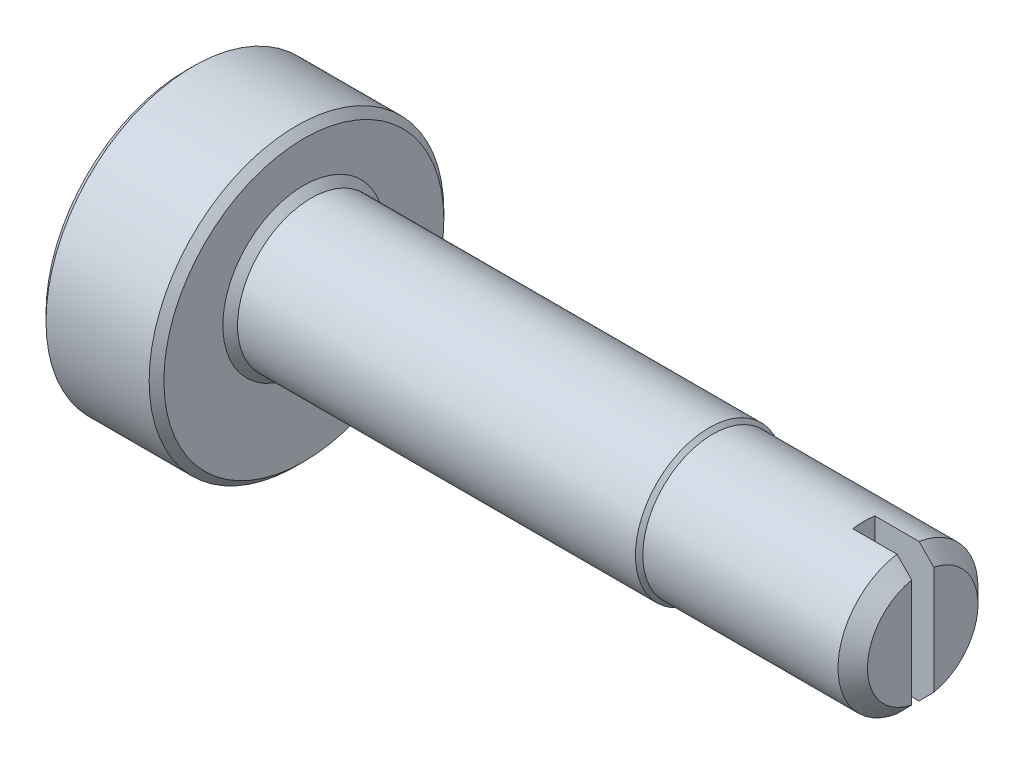
SolidWorks part; units mm, degrees
ref_plane "Спереди" through (0, 0, 0) normal (0, 0, 1) x (1, 0, 0)
ref_plane "Сверху" through (0, 0, 0) normal (0, 1, 0) x (1, 0, 0)
ref_plane "Справа" through (0, 0, 0) normal (1, 0, 0) x (0, 0, -1)
sketch "Эскиз1" plane through (0, 0, 0) normal (0, 0, 1) x (1, 0, 0)
  line L0 (0, 0) -> (0, 2.5)
  line L1 (0, 2.5) -> (1.6, 2.5)
  line L2 (1.6, 2.5) -> (1.6, 1.1)
  line L3 (1.7, 1) -> (7.1, 1)
  line L4 (10, 0.95) -> (10, 0)
  line L5 (10, 0) -> (0, 0)
  line L6 (0, 0) -> (-2.4294, 0) construction
  line L7 (7.1, 1) -> (7.15, 0.95)
  line L8 (7.15, 0.95) -> (10, 0.95)
  line L9 (1.6, 1.1) -> (1.7, 1)
  point P5 (1.6, 1)
  dimension "D1" = 5
  dimension "D2" = 2
  dimension "D3" = 1.6
  dimension "D4" = 10
  dimension "D5" = 1.9
  dimension "D6" = 45
  dimension "D7" = 5.5
  dimension "D10" = 0.1
revolve "Повернуть1" add sketch "Эскиз1" angle 360 about L6
cosmetic thread "Условное изображение резьбы1" parameters "D1"=2.5, "D2"=1.548
sketch "Эскиз2" plane through (0, 0, 0) normal (-1, 0, 0) x (0, 0, 1)
  circle A0 centre (0, -0.25) radius 2
  circle A2 centre (0, 0) radius 2.5 construction
  circle M1 centre (0, 0) radius 2.5
  dimension "D1" = 4
  dimension "D2" = 0.25
extrude "Вырез-Вытянуть5" cut sketch "Эскиз2" against normal up to next contours A0 M1
sketch "Эскиз3" plane through (10, 0, 0) normal (1, 0, 0) x (0, 0, -1)
  line L0 (-0.15, 0.9887) -> (-0.15, -0.9887)
  line L1 (0.15, -0.9887) -> (0.15, 0.9887)
  circle A0 centre (0, 0) radius 1 construction
  circle A1 centre (0, 0) radius 1 construction
  dimension "D1" = 0.3
extrude "Вырез-Вытянуть8" cut sketch "Эскиз3" against normal blind 0.8
chamfer "Фаска1" distance 0.2 angle 45 2 edges at (10, 0, -0.95) (10, 0, 0.95)
chamfer "Фаска2" distance 0.1 angle 45 2 edges at (0, -0.25, 2) (1.6, -0.25, -2)
sketch "Эскиз4" plane through (0, 0, 0) normal (0, 0, 1) x (1, 0, 0)
  line L0 (0.4, -0.25) -> (0.4, -3.0232) construction
  line L1 (0, 1.65) -> (0, -2.15) construction
  circle A0 centre (-3.425, -0.25) radius 3.825
  dimension "D1" = 7.65
  dimension "D2" = 0.25
  dimension "D3" = 0.4
extrude "Вырез-Вытянуть9" cut sketch "Эскиз4" against normal blind 0.25 and the other way blind 0.25
